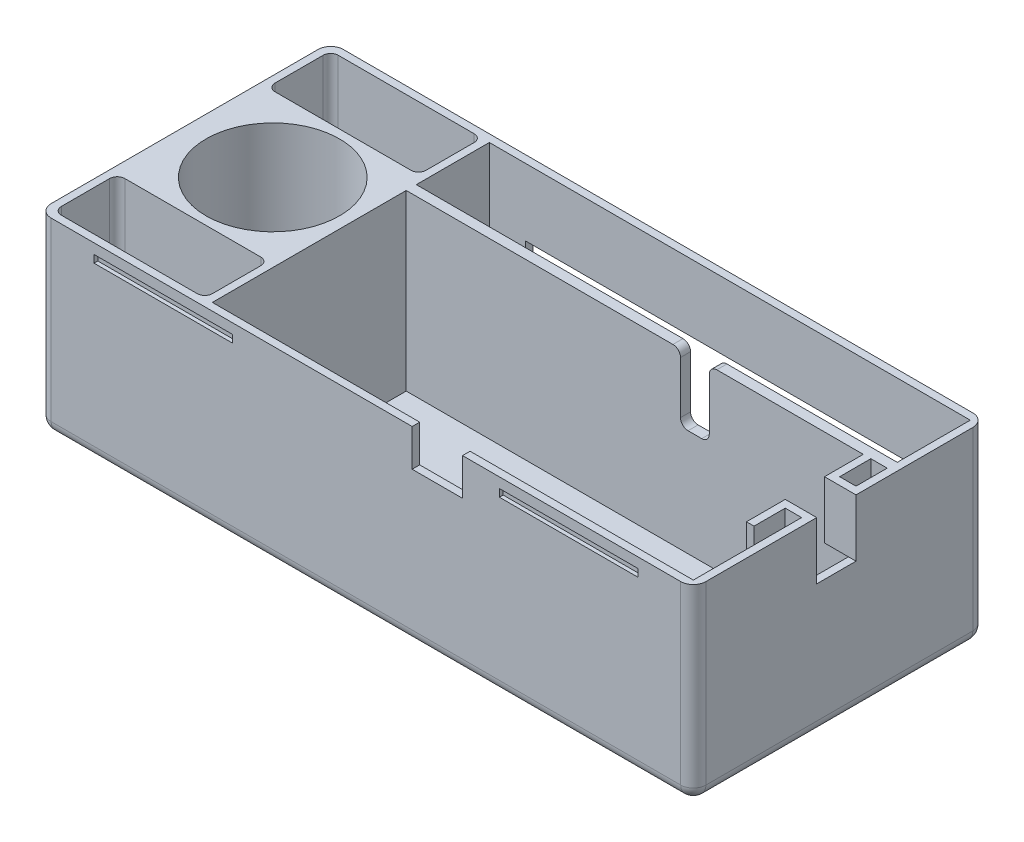
SolidWorks part; units mm, degrees
ref_plane "Front Plane" through (0, 0, 0) normal (0, 0, 1) x (1, 0, 0)
ref_plane "Top Plane" through (0, 0, 0) normal (0, 1, 0) x (1, 0, 0)
ref_plane "Right Plane" through (0, 0, 0) normal (1, 0, 0) x (0, 0, -1)
sketch "Sketch1" plane through (0, 0, 0) normal (0, 1, 0) x (1, 0, 0)
  line L1 (0, 0) -> (260, 0)
  line L2 (0, 0) -> (0, 116)
  line L3 (0, 116) -> (260, 116)
  line L4 (260, 0) -> (260, 116)
  dimension "D1" = 260
  dimension "D2" = 116
extrude "Boss-Extrude1" add sketch "Sketch1" along normal blind 75
sketch "Sketch2" plane through (0, 75, 0) normal (0, 1, 0) x (1, 0, 0)
  line L0 (260, 116) -> (0, 116) construction
  line L1 (257, 113) -> (66, 113)
  line L2 (257, 113) -> (257, 84)
  line L3 (257, 84) -> (66, 84)
  line L4 (66, 113) -> (66, 84)
  line L5 (66, 80) -> (257, 80)
  line L6 (66, 80) -> (66, 3)
  line L7 (66, 3) -> (257, 3)
  line L8 (257, 80) -> (257, 3)
  line L9 (0, 0) -> (260, 0) construction
  line L10 (260, 0) -> (260, 116) construction
  line L11 (0, 116) -> (0, 0) construction
  line L12 (3, 113) -> (63, 113)
  line L13 (3, 113) -> (3, 87.8763)
  line L14 (3, 87.8763) -> (63, 87.8763)
  line L15 (63, 113) -> (63, 87.8763)
  line L16 (3, 28.2327) -> (63, 28.2327)
  line L17 (3, 28.2327) -> (3, 3)
  line L18 (3, 3) -> (63, 3)
  line L19 (63, 28.2327) -> (63, 3)
  circle A0 centre (35, 58) radius 26.5
  dimension "D9" = 53
  dimension "D10" = 31
  dimension "D11" = 58
  dimension "D12" = 58
  dimension "D19" = 4
  dimension "D1" = 191
  dimension "D2" = 191
  dimension "D3" = 77
  dimension "D4" = 29
  dimension "D5" = 3
  dimension "D6" = 3
  dimension "D7" = 3
  dimension "D8" = 3
  dimension "D13" = 3
  dimension "D14" = 3
  dimension "D15" = 3
  dimension "D16" = 3
  dimension "D17" = 3
  dimension "D18" = 3
  dimension "D20" = 35
extrude "Cut-Extrude1" cut sketch "Sketch2" against normal blind 69
fillet "Fillet1" radius 5 4 edges at (260, 37.5, -116) (260, 37.5, 0) (0, 37.5, 0) (0, 37.5, -116)
fillet "Fillet2" radius 5 8 edges at (258.5355, 0, -114.5355) (260, 0, -58) (258.5355, 0, -1.4645) (130, 0, 0) (1.4645, 0, -1.4645) (0, 0, -58) (1.4645, 0, -114.5355) (130, 0, -116)
sketch "Sketch3" plane through (0, 6, 0) normal (0, 1, 0) x (1, 0, 0)
  line L0 (257, 80) -> (66, 80) construction
  line L1 (66, 80) -> (66, 3) construction
  line L2 (66, 3) -> (257, 3) construction
  line L3 (257, 3) -> (257, 80) construction
  line L4 (66, 3) -> (257, 3) construction
  line L5 (257, 3) -> (257, 80) construction
  circle A0 centre (70.8493, 75.15) radius 1.6
  circle A1 centre (70.8493, 7.85) radius 1.6
  circle A2 centre (252.15, 75.15) radius 1.6
  circle A3 centre (252.15, 7.85) radius 1.6
  dimension "D1" = 3.2
  dimension "D2" = 4.85
  dimension "D3" = 4.8493
  dimension "D4" = 4.85
  dimension "D5" = 4.8493
  dimension "D6" = 4.85
  dimension "D7" = 4.85
  dimension "D8" = 4.85
  dimension "D9" = 4.85
sketch "Sketch4" plane through (0, 75, 0) normal (0, 1, 0) x (1, 0, 0)
  line L0 (66, 84) -> (257, 84) construction
  line L1 (186.34, 84) -> (174.91, 84)
  line L2 (186.34, 84) -> (186.34, 80)
  line L3 (186.34, 80) -> (174.91, 80)
  line L4 (174.91, 84) -> (174.91, 80)
  line L5 (257, 80) -> (66, 80) construction
  line L6 (260, 5) -> (260, 111) construction
  dimension "D1" = 73.66
  dimension "D2" = 85.09
extrude "Cut-Extrude3" cut sketch "Sketch4" against normal blind 26.67
fillet "Fillet3" radius 3 4 edges at (186.34, 48.33, -82) (174.91, 48.33, -82) (186.34, 75, -82) (174.91, 75, -82)
sketch "Sketch5" plane through (0, 0, 0) normal (0, 0, 1) x (1, 0, 0)
  line L0 (0, 5) -> (0, 75) construction
  line L1 (22, 71) -> (77, 71)
  line L2 (22, 71) -> (22, 68)
  line L3 (22, 68) -> (77, 68)
  line L4 (77, 71) -> (77, 68)
  line L5 (5, 75) -> (255, 75) construction
  line L6 (260, 75) -> (260, 5) construction
  line L7 (183, 71) -> (238, 71)
  line L8 (183, 71) -> (183, 68)
  line L9 (183, 68) -> (238, 68)
  line L10 (238, 71) -> (238, 68)
  dimension "D1" = 22
  dimension "D2" = 4
  dimension "D3" = 3
  dimension "D4" = 55
  dimension "D5" = 3
  dimension "D6" = 55
  dimension "D7" = 22
  dimension "D8" = 4
extrude "Cut-Extrude4" cut sketch "Sketch5" against normal blind 1.5
sketch "Sketch6" plane through (0, 0, -116) normal (0, 0, -1) x (-1, 0, 0)
  line L0 (0, 75) -> (0, 5) construction
  line L1 (-238, 71) -> (-183, 71)
  line L2 (-238, 71) -> (-238, 68)
  line L3 (-238, 68) -> (-183, 68)
  line L4 (-183, 71) -> (-183, 68)
  line L5 (-77, 71) -> (-22, 71)
  line L6 (-77, 71) -> (-77, 68)
  line L7 (-77, 68) -> (-22, 68)
  line L8 (-22, 71) -> (-22, 68)
  line L9 (-260, 5) -> (-260, 75) construction
  line L10 (-255, 75) -> (-5, 75) construction
  dimension "D1" = 55
  dimension "D2" = 55
  dimension "D3" = 22
  dimension "D4" = 22
  dimension "D5" = 3
  dimension "D6" = 3
  dimension "D7" = 4
  dimension "D8" = 4
extrude "Cut-Extrude5" cut sketch "Sketch6" against normal blind 1.5
fillet "Fillet4" radius 3 8 edges at (3, 40.5, -113) (3, 40.5, -87.8763) (63, 40.5, -113) (63, 40.5, -87.8763) (3, 40.5, -28.2327) (63, 40.5, -28.2327) (3, 40.5, -3) (63, 40.5, -3)
sketch "Sketch7" plane through (0, 0, -116) normal (0, 0, -1) x (-1, 0, 0)
  line L0 (-255, 75) -> (-5, 75) construction
  line L1 (-242.649, 48.33) -> (-80.35, 48.33)
  line L2 (-242.649, 48.33) -> (-242.649, 8.452)
  line L3 (-242.649, 8.452) -> (-80.35, 8.452)
  line L4 (-80.35, 48.33) -> (-80.35, 8.452)
  dimension "D1" = 26.67
  dimension "D2" = 39.878
  dimension "D3" = 14.351
  dimension "D4" = 14.35
extrude "Cut-Extrude6" cut sketch "Sketch7" against normal blind 10
sketch "Sketch8" plane through (0, 8.452, 0) normal (0, 1, 0) x (1, 0, 0)
  line L0 (255, 116) -> (5, 116) construction
  line L1 (145.1574, 116) -> (161.5, 116)
  line L2 (145.1574, 116) -> (145.1574, 113)
  line L3 (145.1574, 113) -> (161.5, 113)
  line L4 (161.5, 116) -> (161.5, 113)
  line L5 (257, 113) -> (66, 113) construction
  line L6 (66, 113) -> (66, 84) construction
  dimension "D1" = 79.1574
sketch "Sketch9" plane through (0, 75, 0) normal (0, 1, 0) x (1, 0, 0)
  line L0 (66, 3) -> (257, 3) construction
  line L1 (148.35, 3) -> (168.35, 3)
  line L2 (148.35, 3) -> (148.35, 0)
  line L3 (148.35, 0) -> (168.35, 0)
  line L4 (168.35, 3) -> (168.35, 0)
  line L5 (5, 0) -> (255, 0) construction
  line L6 (260, 5) -> (260, 111) construction
  dimension "D1" = 20
  dimension "D2" = 91.65
extrude "Cut-Extrude7" cut sketch "Sketch9" against normal blind 14.7
sketch "Sketch10" plane through (0, 75, 0) normal (0, 1, 0) x (1, 0, 0)
  line L0 (257, 3) -> (257, 80) construction
  line L1 (257, 64.61) -> (260, 64.61)
  line L2 (257, 64.61) -> (257, 49.01)
  line L3 (257, 49.01) -> (260, 49.01)
  line L4 (260, 64.61) -> (260, 49.01)
  line L5 (260, 5) -> (260, 111) construction
  line L6 (257, 80) -> (189.34, 80) construction
  dimension "D1" = 15.6
  dimension "D2" = 15.39
extrude "Cut-Extrude8" cut sketch "Sketch10" against normal blind 22.8
sketch "Sketch11" plane through (257, 0, 0) normal (-1, 0, 0) x (0, 0, 1)
  line L0 (-64.61, 52.2) -> (-49.01, 52.2) construction
  line L1 (-49.01, 75) -> (-46.01, 75)
  line L2 (-49.01, 75) -> (-49.01, 52.2)
  line L3 (-49.01, 52.2) -> (-46.01, 52.2)
  line L4 (-46.01, 75) -> (-46.01, 52.2)
  line L6 (-64.61, 75) -> (-67.61, 75)
  line L7 (-64.61, 75) -> (-64.61, 52.2)
  line L8 (-64.61, 52.2) -> (-67.61, 52.2)
  line L9 (-67.61, 75) -> (-67.61, 52.2)
  dimension "D1" = 0
  dimension "D2" = 3
  dimension "D3" = 3
  dimension "D4" = 0
extrude "Boss-Extrude2" add sketch "Sketch11" along normal blind 6.5
sketch "Sketch12" plane through (250.5, 0, 0) normal (-1, 0, 0) x (0, 0, 1)
  line L0 (-49.01, 52.2) -> (-46.01, 52.2) construction
  line L1 (-64.61, 75) -> (-80, 75)
  line L2 (-64.61, 75) -> (-64.61, 52.2)
  line L3 (-64.61, 52.2) -> (-80, 52.2)
  line L4 (-80, 75) -> (-80, 52.2)
  line L5 (-49.01, 75) -> (-33.62, 75)
  line L6 (-49.01, 75) -> (-49.01, 52.2)
  line L7 (-49.01, 52.2) -> (-33.62, 52.2)
  line L8 (-33.62, 75) -> (-33.62, 52.2)
  line L9 (-67.61, 52.2) -> (-64.61, 52.2) construction
  dimension "D1" = 0
  dimension "D2" = 0
  dimension "D3" = 15.39
  dimension "D4" = 15.39
extrude "Boss-Extrude3" add sketch "Sketch12" along normal blind 3
sketch "Sketch13" plane through (0, 6, 0) normal (0, 1, 0) x (1, 0, 0)
  circle A0 centre (35, 58) radius 12.5
  dimension "D1" = 25
extrude "Cut-Extrude9" cut sketch "Sketch13" against normal blind 3
